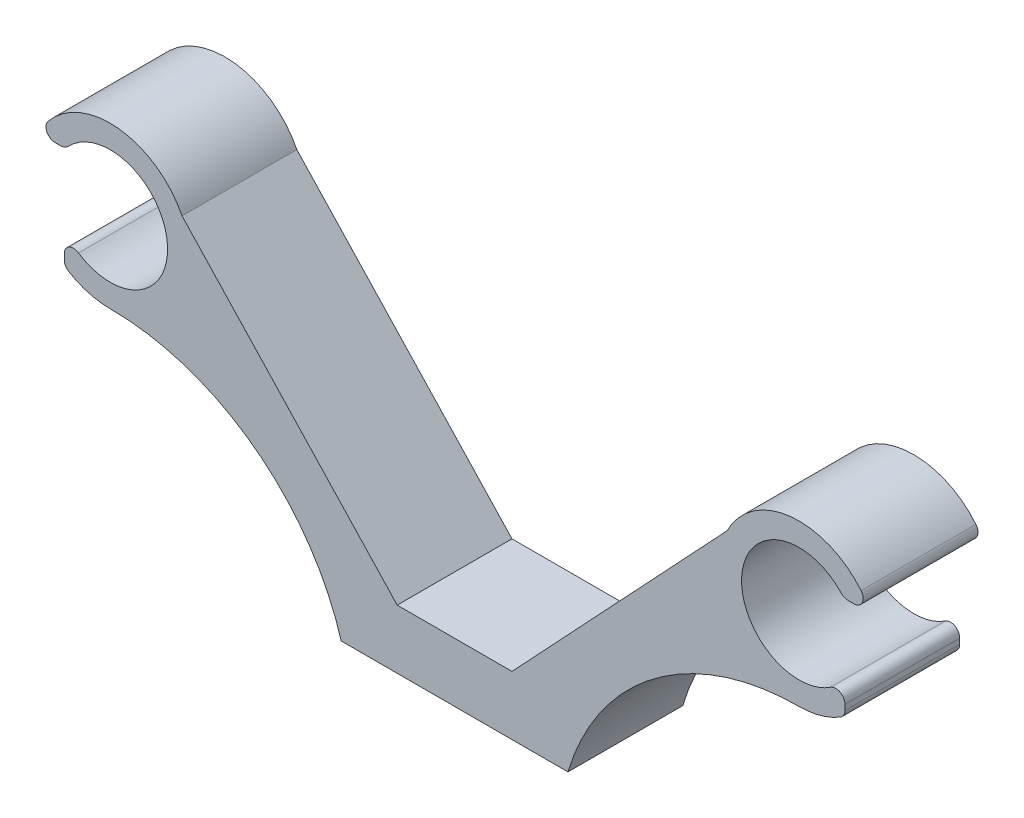
SolidWorks part; units mm, degrees
ref_plane "Front Plane" through (0, 0, 0) normal (0, 0, 1) x (1, 0, 0)
ref_plane "Top Plane" through (0, 0, 0) normal (0, 1, 0) x (1, 0, 0)
ref_plane "Right Plane" through (0, 0, 0) normal (1, 0, 0) x (0, 0, -1)
sketch "Sketch1" plane through (0, 0, 0) normal (0, 0, 1) x (1, 0, 0)
  line L0 (9.8754, 0) -> (-9.8754, 0)
  line L1 (5, 5.1454) -> (-5, 5.1454)
  line L3 (-5, 5.1454) -> (-23.741, 25.1346)
  line L4 (34.348, 25.1346) -> (34.7916, 25.1346)
  line L5 (-34, 16.6896) -> (-34, 17.1626)
  line L6 (-34.348, 25.1346) -> (-34.7916, 25.1346)
  line L7 (34, 16.6896) -> (34, 17.1626)
  line L8 (5, 5.1454) -> (23.741, 25.1346)
  arc A0 (-32.7586, 17.8299) -> (-33.6234, 25.4455) centre (-30, 22) ccw
  arc A1 (-9.8754, 0) -> (-30, 15) centre (-30, -6) ccw
  arc A2 (-33.6129, 16.0044) -> (-30, 15) centre (-30, 22) ccw
  arc A3 (-23.741, 25.1346) -> (-35.4099, 26.4422) centre (-30, 22) ccw
  arc A4 (-34.348, 25.1346) -> (-33.6234, 25.4455) centre (-34.348, 26.1346) ccw
  arc A5 (-34.7916, 25.1346) -> (-35.4099, 26.4422) centre (-34.7916, 25.9346) cw
  arc A6 (-34, 16.6896) -> (-33.6129, 16.0044) centre (-33.2, 16.6896) ccw
  arc A7 (-34, 17.1626) -> (-32.7586, 17.8299) centre (-33.2, 17.1626) cw
  arc A8 (34, 17.1626) -> (32.7586, 17.8299) centre (33.2, 17.1626) ccw
  arc A9 (34, 16.6896) -> (33.6129, 16.0044) centre (33.2, 16.6896) cw
  arc A10 (34.7916, 25.1346) -> (35.4099, 26.4422) centre (34.7916, 25.9346) ccw
  arc A11 (34.348, 25.1346) -> (33.6234, 25.4455) centre (34.348, 26.1346) cw
  arc A12 (23.741, 25.1346) -> (35.4099, 26.4422) centre (30, 22) cw
  arc A13 (33.6129, 16.0044) -> (30, 15) centre (30, 22) cw
  arc A14 (9.8754, 0) -> (30, 15) centre (30, -6) cw
  arc A15 (32.7586, 17.8299) -> (33.6234, 25.4455) centre (30, 22) cw
  dimension "D4" = 4
  dimension "D5" = 1
  dimension "D6" = 0.8
  dimension "D7" = 0.8
extrude "Boss-Extrude1" add sketch "Sketch1" along normal blind 10
